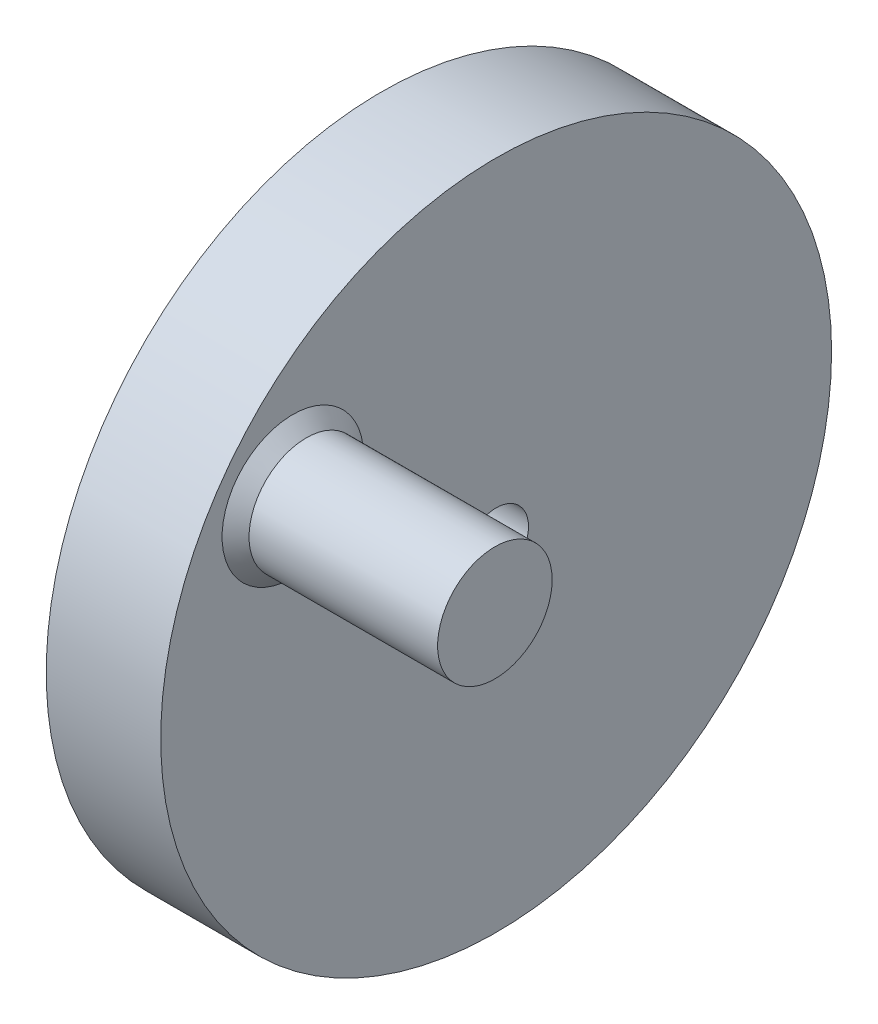
SolidWorks part; units mm, degrees
ref_plane "Alzado" through (0, 0, 0) normal (0, 0, 1) x (1, 0, 0)
ref_plane "Planta" through (0, 0, 0) normal (0, 1, 0) x (1, 0, 0)
ref_plane "Vista lateral" through (0, 0, 0) normal (1, 0, 0) x (0, 0, -1)
sketch "Croquis1" plane through (0, 0, 0) normal (1, 0, 0) x (0, 0, -1)
  circle A0 centre (0, 0) radius 24.9
  circle A1 centre (0, 0) radius 2.4
  dimension "D1" = 49.8
  dimension "D2" = 4.8
extrude "Saliente-Extruir1" add sketch "Croquis1" along normal blind 8.5
sketch "Croquis2" plane through (8.5, 0, 0) normal (1, 0, 0) x (0, 0, -1)
  circle A0 centre (-15.0939, 10.697) radius 4.25
  dimension "D2" = 8.5
  dimension "D1" = 18.5
extrude "Saliente-Extruir2" add sketch "Croquis2" along normal blind 15
chamfer "Chaflán1" distance 1 angle 45 1 edges at (8.5, 10.697, 10.8439)
